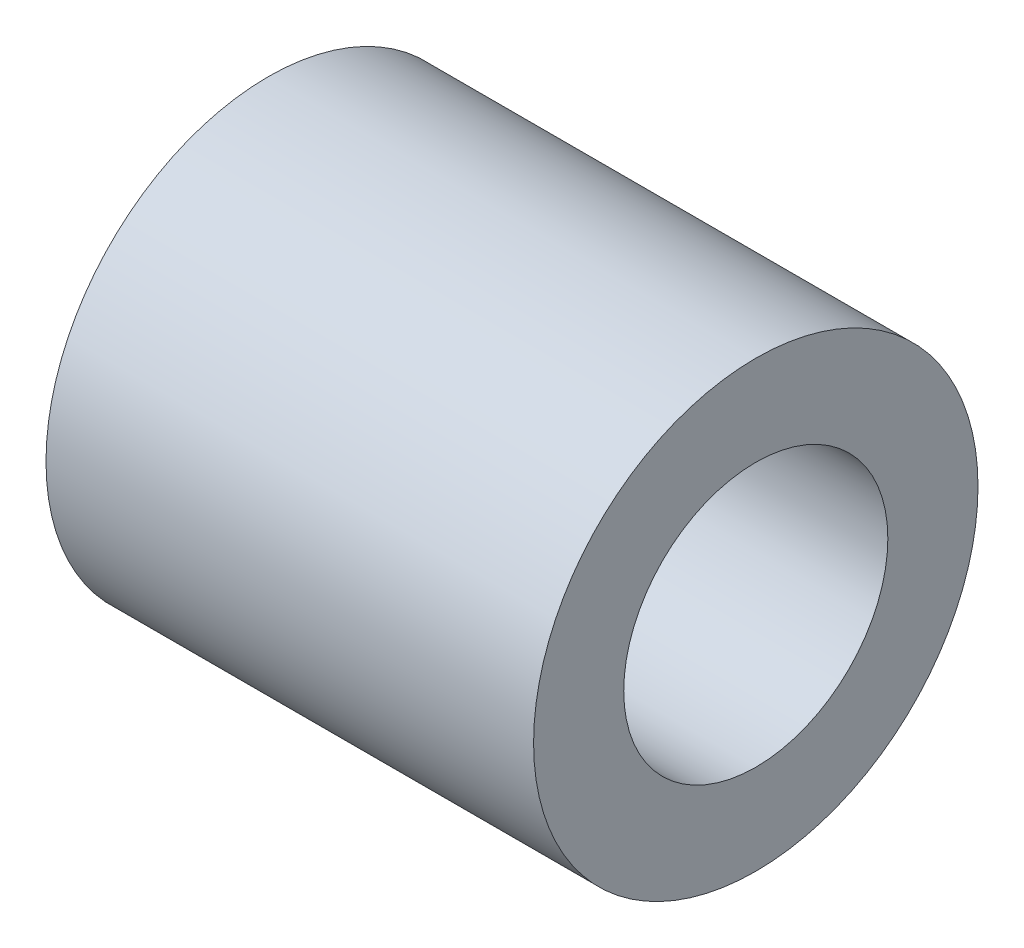
SolidWorks part; units mm, degrees
material "Nylon 101"
ref_plane "Front Plane" through (0, 0, 0) normal (0, 0, 1) x (1, 0, 0)
ref_plane "Top Plane" through (0, 0, 0) normal (0, 1, 0) x (1, 0, 0)
ref_plane "Right Plane" through (0, 0, 0) normal (1, 0, 0) x (0, 0, -1)
sketch "Sketch1" plane through (0, 0, 0) normal (1, 0, 0) x (0, 0, -1)
  circle A0 centre (0, 0) radius 3.302
  circle A1 centre (0, 0) radius 5.5562
  dimension "D1" = 6.604
  dimension "D2" = 11.1125
extrude "Boss-Extrude1" add sketch "Sketch1" along normal blind 12.192
